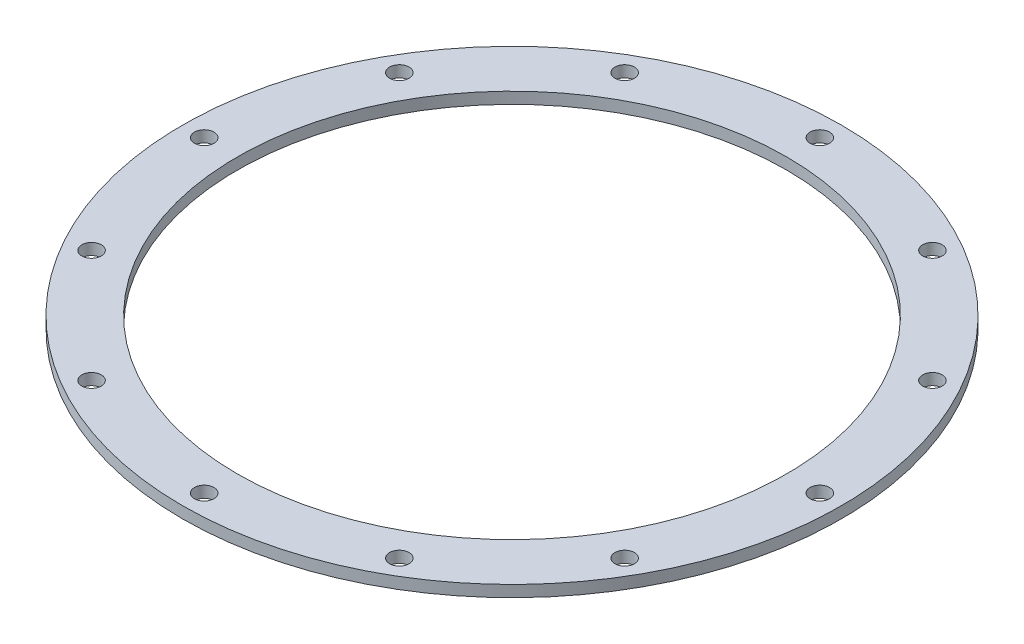
SolidWorks part; units mm, degrees
material "PTFE (general)"
ref_plane "Front Plane" through (0, 0, 0) normal (0, 0, 1) x (1, 0, 0)
ref_plane "Top Plane" through (0, 0, 0) normal (0, 1, 0) x (1, 0, 0)
ref_plane "Right Plane" through (0, 0, 0) normal (1, 0, 0) x (0, 0, -1)
ref_axis "Axis1" through (0, 55, 0) along (0, -1, 0)
sketch "Sketch1" plane through (0, 0, 0) normal (0, 0, 1) x (1, 0, 0)
  line L0 (-38.1, 0) -> (0, 0) construction
  line L1 (-38.1, 0) -> (-45.72, 0)
  line L2 (-38.1, 0) -> (-38.1, 1.5875)
  line L3 (-38.1, 1.5875) -> (-45.72, 1.5875)
  line L4 (-45.72, 0) -> (-45.72, 1.5875)
  line L7 (0, 1.5875) -> (-38.1, 1.5875) construction
  point P12 (-45.72, 0)
  point P18 (-38.1, 1.5875)
revolve "Main" add sketch "Sketch1" angle 360 about axis through (0, 55, 0) along (0, -1, 0)
sketch "Hole Location" plane through (0, 0, 0) normal (0, 1, 0) x (1, 0, 0)
  line L0 (0, 0) -> (-42.7006, 0) construction
  circle A0 centre (0, 0) radius 42.7006 construction
  dimension "D1" = 85.4012
hole_wizard "#36 (0.1065) Diameter Hole1" positions "Sketch3" profile "Sketch5" hole size "#36" standard "ANSI Inch" end condition through all
sketch "Sketch3" plane through (0, 0, 0) normal (0, -1, 0) x (-1, 0, 0)
  point P0 (42.7006, 0)
sketch "Sketch5" plane through (-42.7006, 0, 0) normal (1, 0, 0) x (0, 0, -1)
  line L0 (0, 0) -> (0, 1.5875)
  line L1 (0, 1.5875) -> (1.3525, 1.5875)
  line L2 (1.3525, 1.5875) -> (1.3525, 0)
  line L5 (1.3525, 0) -> (0, 0)
  line L11 (0, -6.35) -> (0, 107.95) construction
  dimension "Thru Hole Dia." = 2.7051
  dimension "Thru Hole Depth" = 1.5875
pattern_circular "Screw Passthroughs" count 12 over 360 about axis through (0, 0, 0) along (0, 1, 0) of "#36 (0.1065) Diameter Hole1"
equation "\"D1@Hole Location\"=\"TANK DIAMETER@Cryo Tank.Assembly\"+\"GASKET SEAT THICKNESS@Cryo Tank.Assembly\"+\"LINER THICKNESS@Cryo Tank.Assembly\"+\"ALUMINUM LAP THICKNESS@Cryo Tank.Assembly\""
